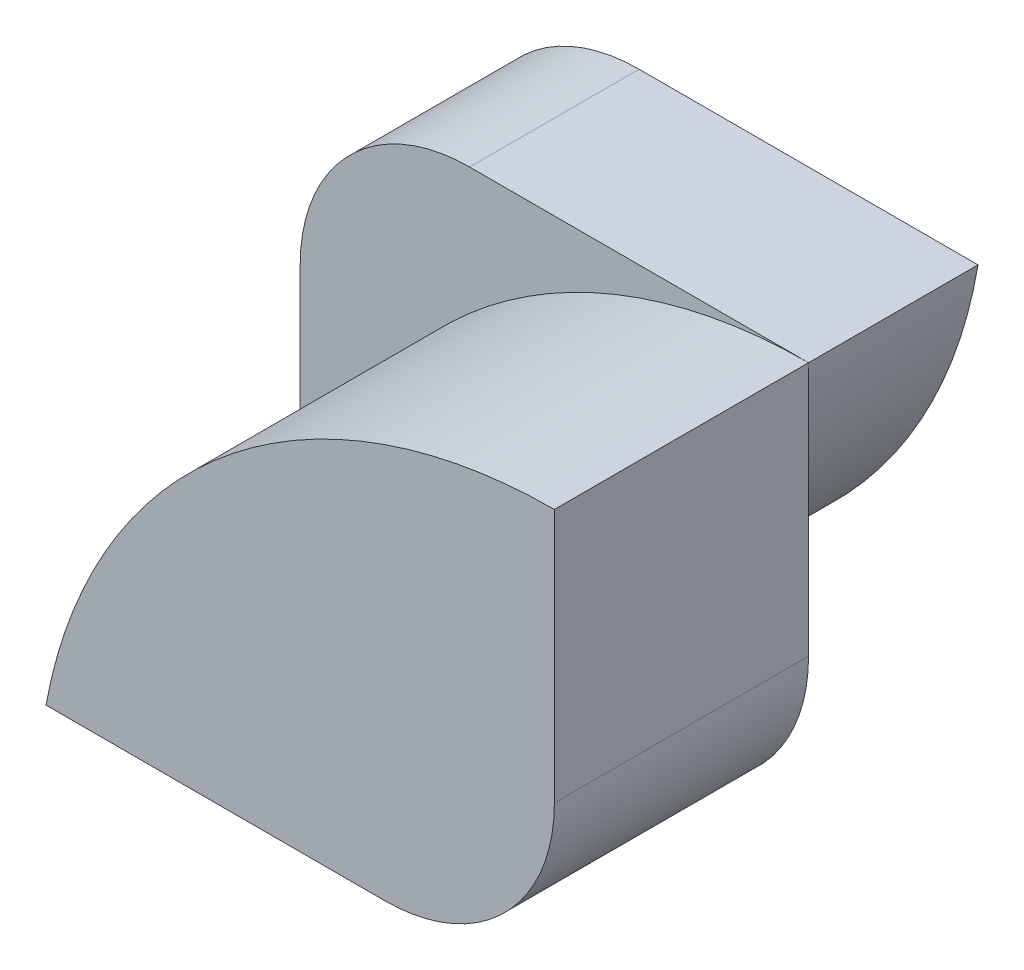
SolidWorks part; units mm, degrees
ref_plane "Front Plane" through (0, 0, 0) normal (0, 0, 1) x (1, 0, 0)
ref_plane "Top Plane" through (0, 0, 0) normal (0, 1, 0) x (1, 0, 0)
ref_plane "Right Plane" through (0, 0, 0) normal (1, 0, 0) x (0, 0, -1)
sketch "Sketch1" plane through (0, 0, 0) normal (0, 0, 1) x (1, 0, 0)
  line L0 (0, 0) -> (-20, 0)
  line L1 (-30, -10) -> (-30, -25)
  arc A0 (-20, 0) -> (-30, -10) centre (-20, -10) ccw
  arc A1 (-30, -25) -> (0, 0) centre (-29.5809, 4.9971) ccw
  dimension "D1" = 30
  dimension "D4" = 10
  dimension "D2" = 20
  dimension "D3" = 15
extrude "Boss-Extrude1" add sketch "Sketch1" along normal blind 10
sketch "Sketch2" plane through (0, 0, 10) normal (0, 0, 1) x (1, 0, 0)
  line L0 (0, 0) -> (0, -15)
  line L2 (-10, -25) -> (-30, -25)
  arc A0 (-30, -25) -> (0, 0) centre (0, -30.5) cw
  arc A1 (-10, -25) -> (0, -15) centre (-10, -15) ccw
  dimension "D2" = 15
  dimension "D1" = 20
extrude "Boss-Extrude2" add sketch "Sketch2" along normal blind 15
